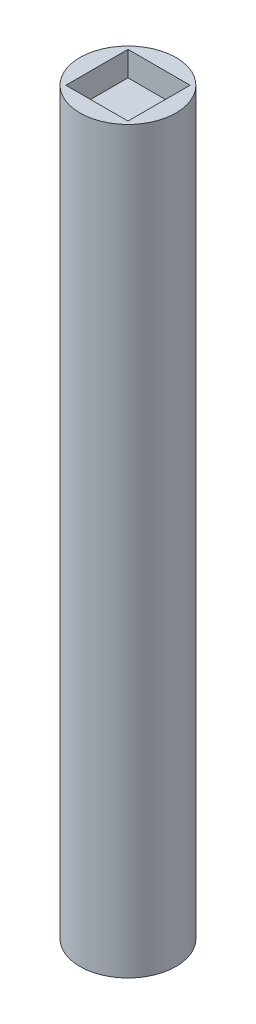
SolidWorks part; units mm, degrees
ref_plane "Front Plane" through (0, 0, 0) normal (0, 0, 1) x (1, 0, 0)
ref_plane "Top Plane" through (0, 0, 0) normal (0, 1, 0) x (1, 0, 0)
ref_plane "Right Plane" through (0, 0, 0) normal (1, 0, 0) x (0, 0, -1)
sketch "Sketch1" plane through (0, 0, 0) normal (0, 1, 0) x (1, 0, 0)
  circle A0 centre (0, 0) radius 4.875
  dimension "D1" = 9.75
extrude "Boss-Extrude1" add sketch "Sketch1" along normal mid plane 75
sketch "Sketch2" plane through (0, 37.5, 0) normal (0, 1, 0) x (1, 0, 0)
  line L0 (-3.15, 3.15) -> (3.15, 3.15)
  line L1 (-3, -3) -> (3, -3) construction
  line L2 (-3, -3) -> (-3, 3) construction
  line L3 (-3, 3) -> (3, 3) construction
  line L4 (3, -3) -> (3, 3) construction
  line L5 (-3, -3) -> (3, 3) construction
  line L6 (-3, 3) -> (3, -3) construction
  line L7 (3.15, -3.15) -> (3.15, 3.15)
  line L8 (-3.15, -3.15) -> (3.15, -3.15)
  line L9 (-3.15, -3.15) -> (-3.15, 3.15)
  point P0 (0, 0)
  dimension "D1" = 6
  dimension "D2" = 0.15
extrude "Boss-Extrude2" add sketch "Sketch2" along normal blind 2.5
sketch "Sketch3" plane through (0, 40, 0) normal (0, 1, 0) x (1, 0, 0)
  line L4 (-3.15, 3.15) -> (-3.15, -3.15)
  line L5 (-3.15, 3.15) -> (-3.15, -3.15)
  line L6 (-3.15, -3.15) -> (3.15, -3.15)
  line L7 (-3.15, -3.15) -> (3.15, -3.15)
  line L12 (3.15, -3.15) -> (3.15, 3.15)
  line L13 (3.15, -3.15) -> (3.15, 3.15)
  line L14 (3.15, 3.15) -> (-3.15, 3.15)
  line L15 (3.15, 3.15) -> (-3.15, 3.15)
  dimension "D1" = 0
extrude "Cut-Extrude1" cut sketch "Sketch3" against normal blind 5
